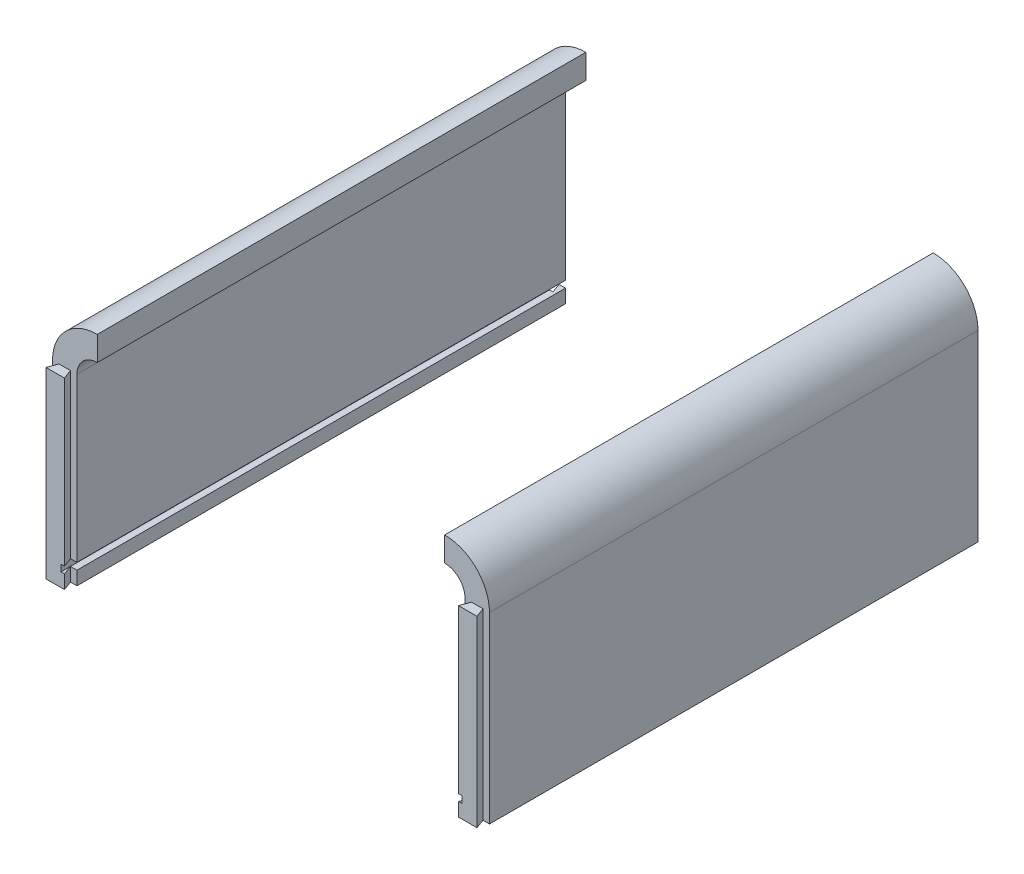
SolidWorks part; units mm, degrees
ref_plane "前基準面" through (0, 0, 0) normal (0, 0, 1) x (1, 0, 0)
ref_plane "上基準面" through (0, 0, 0) normal (0, 1, 0) x (1, 0, 0)
ref_plane "右基準面" through (0, 0, 0) normal (1, 0, 0) x (0, 0, -1)
sketch "草圖1" plane through (0, 0, 0) normal (0, 0, 1) x (1, 0, 0)
  line L0 (0, 26.1756) -> (0, -67.2488) construction
  line L1 (28.6, -25.249) -> (28.6, -49.249)
  line L6 (32.2, -25.249) -> (32.2, -52.249)
  line L7 (32.2, -52.249) -> (28.6, -52.249)
  line L14 (-25.6, -22.249) -> (-25.6, -18.649)
  line L15 (-32.2, -52.249) -> (-28.6, -52.249)
  line L16 (-32.2, -25.249) -> (-32.2, -52.249)
  line L17 (25.6, -22.249) -> (25.6, -18.649)
  line L18 (-28.6, -25.249) -> (-28.6, -49.249)
  line L19 (28.6, -49.249) -> (29.56, -49.249)
  line L20 (29.56, -49.249) -> (29.56, -50.249)
  line L21 (29.56, -50.249) -> (28.6, -50.249)
  line L22 (28.6, -50.249) -> (28.6, -52.249)
  line L23 (-29.56, -50.249) -> (-28.6, -50.249)
  line L24 (-29.56, -49.249) -> (-29.56, -50.249)
  line L25 (-28.6, -49.249) -> (-29.56, -49.249)
  line L26 (-28.6, -50.249) -> (-28.6, -52.249)
  arc A1 (28.6, -25.249) -> (25.6, -22.249) centre (25.6, -25.249) ccw
  arc A2 (25.6, -18.649) -> (32.2, -25.249) centre (25.6, -25.249) cw
  arc A3 (-25.6, -18.649) -> (-32.2, -25.249) centre (-25.6, -25.249) ccw
  arc A4 (-28.6, -25.249) -> (-25.6, -22.249) centre (-25.6, -25.249) cw
  dimension "D5" = 3.6
  dimension "D6" = 0.96
  dimension "D1" = 28.6
  dimension "D2" = 27
  dimension "D3" = 3.6
  dimension "D4" = 3
  dimension "D7" = 1
extrude "填料-伸長4" add sketch "草圖1" along normal blind 72
sketch "草圖3" plane through (0, -52.249, 0) normal (0, -1, 0) x (1, 0, 0)
  line L0 (-30.4, 74.152) -> (-30.4, 73.4) construction
  line L1 (-31.25, 72) -> (-31.7596, 73.4)
  line L2 (-32.2, 72) -> (-28.6, 72) construction
  line L3 (-31.7596, 73.4) -> (-29.0404, 73.4)
  line L4 (-31.25, 72) -> (-29.55, 72)
  line L6 (-29.55, 72) -> (-29.0404, 73.4)
  line L7 (-30.4, 72) -> (-30.4, 70.5482) construction
  line L8 (0, -23.7865) -> (0, 84.514) construction
  line L9 (29.55, 72) -> (29.0404, 73.4)
  line L10 (31.25, 72) -> (29.55, 72)
  line L11 (31.7596, 73.4) -> (29.0404, 73.4)
  line L12 (31.25, 72) -> (31.7596, 73.4)
  dimension "D1" = 0.95
  dimension "D2" = 70
  dimension "D3" = 1.4
extrude "填料-伸長5" add sketch "草圖3" against normal blind 27
sketch "草圖4" plane through (0, 0, 73.4) normal (0, 0, 1) x (1, 0, 0)
  line L0 (-29.56, -49.249) -> (-29.0404, -49.249)
  line L1 (-29.0404, -25.249) -> (-29.0404, -52.249) construction
  line L2 (-29.55, -49.249) -> (-28.6, -49.249) construction
  line L3 (-29.0404, -49.249) -> (-29.0404, -50.249)
  line L4 (-28.6, -50.249) -> (-29.55, -50.249) construction
  line L5 (-29.0404, -50.249) -> (-29.56, -50.249)
  line L6 (-29.55, -50.249) -> (-29.56, -50.249) construction
  line L7 (-29.56, -50.249) -> (-29.56, -49.249)
  line L8 (0, 10.6208) -> (0, -70.9226) construction
  line L9 (29.56, -50.249) -> (29.56, -49.249)
  line L10 (29.0404, -50.249) -> (29.56, -50.249)
  line L11 (29.0404, -49.249) -> (29.0404, -50.249)
  line L12 (29.56, -49.249) -> (29.0404, -49.249)
extrude "除料-伸長2" cut sketch "草圖4" against normal blind 1.4
sketch "草圖5" plane through (0, -52.249, 0) normal (0, -1, 0) x (1, 0, 0)
  line L0 (-30.4, 0) -> (-30.4, -4.0618) construction
  line L1 (-32.2, 0) -> (-28.6, 0) construction
  line L2 (-31.25, 0) -> (-31.7596, 1.4)
  line L3 (-31.7596, 1.4) -> (-29.0404, 1.4)
  line L5 (-29.55, 0) -> (-31.25, 0)
  line L6 (-29.55, 0) -> (-29.0404, 1.4)
  line L7 (0, -14.0478) -> (0, 21.8204) construction
  line L8 (29.55, 0) -> (29.0404, 1.4)
  line L9 (29.55, 0) -> (31.25, 0)
  line L10 (31.7596, 1.4) -> (29.0404, 1.4)
  line L11 (31.25, 0) -> (31.7596, 1.4)
  line L12 (-32.2, 72) -> (-32.2, 0) construction
  dimension "D1" = 1.4
  dimension "D2" = 70
  dimension "D3" = 0.95
extrude "除料-伸長4" cut sketch "草圖5" against normal blind 27
